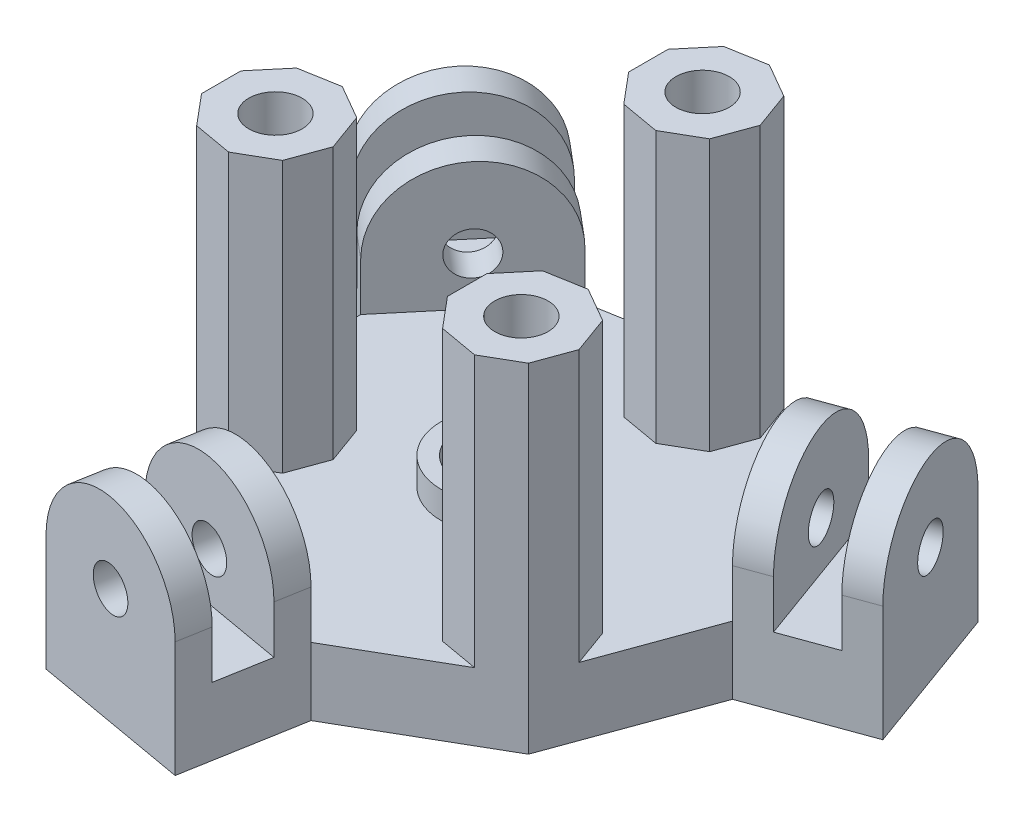
SolidWorks part; units mm, degrees
ref_plane "Front Plane" through (0, 0, 0) normal (0, 0, 1) x (1, 0, 0)
ref_plane "Top Plane" through (0, 0, 0) normal (0, 1, 0) x (1, 0, 0)
ref_plane "Right Plane" through (0, 0, 0) normal (1, 0, 0) x (0, 0, -1)
sketch "Sketch1" plane through (0, 0, 0) normal (0, 1, 0) x (1, 0, 0)
  line L0 (-20.5, -7.4614) -> (-10.9078, -18.8929)
  line L1 (16.7118, -14.0228) -> (21.8156, 0)
  line L2 (21.8156, 0) -> (16.7118, 14.0228)
  line L3 (16.7118, 14.0228) -> (3.7882, 21.4842)
  line L4 (3.7882, 21.4842) -> (-10.9078, 18.8929)
  line L5 (-10.9078, 18.8929) -> (-20.5, 7.4614)
  line L6 (-20.5, 7.4614) -> (-20.5, -7.4614)
  line L7 (-10.9078, -18.8929) -> (3.7882, -21.4842)
  line L8 (3.7882, -21.4842) -> (16.7118, -14.0228)
  line L9 (16.7118, 14.0228) -> (21.8156, 0)
  line L10 (16.7118, 14.0228) -> (27.0484, 17.785)
  line L11 (21.8156, 0) -> (32.1523, 3.7622)
  line L12 (27.0484, 17.785) -> (32.1523, 3.7622)
  line L13 (3.7882, -21.4842) -> (-10.9078, -18.8929)
  line L14 (3.7882, -21.4842) -> (1.8781, -32.3171)
  line L15 (-10.9078, -18.8929) -> (-12.818, -29.7258)
  line L16 (1.8781, -32.3171) -> (-12.818, -29.7258)
  line L17 (-20.5, 7.4614) -> (-10.9078, 18.8929)
  line L18 (-20.5, 7.4614) -> (-28.9265, 14.5321)
  line L19 (-10.9078, 18.8929) -> (-19.3343, 25.9636)
  line L20 (-28.9265, 14.5321) -> (-19.3343, 25.9636)
  circle A0 centre (0, 0) radius 20.5 construction
  circle A1 centre (0, 0) radius 4.1
  dimension "D1" = 41
  dimension "D2" = 8.2
  dimension "D3" = 11
extrude "Boss-Extrude1" add sketch "Sketch1" along normal blind 6.35 contours L16 L14 L7 L15 | L7 L8 L1 L2 L3 L4 L5 L6 L0 A1 | L12 L10 L2 L11 | L20 L18 L5 L19
ref_plane "Plane1" through (-5.4699, 0, 31.0214) normal (0.1736, 0, -0.9848) x (-0.9848, 0, -0.1736)
sketch "Sketch4" plane through (-5.4699, 0, 31.0214) normal (0.1736, 0, -0.9848) x (-0.9848, 0, -0.1736)
  line L0 (-7.4614, 6.35) -> (-7.4614, 10.85)
  line L1 (7.4614, 6.35) -> (7.4614, 10.85)
  line L2 (-7.4614, 6.35) -> (7.4614, 6.35)
  arc A0 (7.4614, 10.85) -> (-7.4614, 10.85) centre (0, 10.85) ccw
  circle A1 centre (0, 10.85) radius 2
  dimension "D2" = 4
  dimension "D1" = 4.5
extrude "Boss-Extrude2" add sketch "Sketch4" along normal blind 3
ref_plane "Plane2" through (-3.5598, 0, 20.1886) normal (0.1736, 0, -0.9848) x (-0.9848, 0, -0.1736)
sketch "Sketch6" plane through (-3.5598, 0, 20.1886) normal (0.1736, 0, -0.9848) x (-0.9848, 0, -0.1736)
  line L0 (-7.4614, 6.35) -> (-7.4614, 10.85)
  line L1 (7.4614, 6.35) -> (7.4614, 10.85)
  line L2 (-7.4614, 6.35) -> (7.4614, 6.35)
  arc A0 (7.4614, 10.85) -> (-7.4614, 10.85) centre (0, 10.85) ccw
  circle A1 centre (0, 10.85) radius 2
  dimension "D2" = 4
  dimension "D1" = 4.5
extrude "Boss-Extrude4" add sketch "Sketch6" against normal blind 3
ref_plane "Plane3" through (29.6003, 0, -10.7736) normal (-0.9397, 0, 0.342) x (0.342, 0, 0.9397)
sketch "Sketch8" plane through (29.6003, 0, -10.7736) normal (-0.9397, 0, 0.342) x (0.342, 0, 0.9397)
  line L0 (-7.4614, 10.85) -> (-7.4614, 6.35)
  line L1 (-7.4614, 6.35) -> (7.4614, 6.35)
  line L2 (7.4614, 6.35) -> (7.4614, 10.85)
  arc A0 (7.4614, 10.85) -> (-7.4614, 10.85) centre (0, 10.85) ccw
  circle A1 centre (0, 10.85) radius 2
  dimension "D2" = 4
  dimension "D1" = 4.5
extrude "Boss-Extrude5" add sketch "Sketch8" along normal blind 3
ref_plane "Plane4" through (19.2637, 0, -7.0114) normal (-0.9397, 0, 0.342) x (0.342, 0, 0.9397)
sketch "Sketch9" plane through (19.2637, 0, -7.0114) normal (-0.9397, 0, 0.342) x (0.342, 0, 0.9397)
  line L0 (-7.4614, 6.35) -> (-7.4614, 10.85)
  line L1 (-7.4614, 6.35) -> (7.4614, 6.35)
  line L2 (7.4614, 6.35) -> (7.4614, 10.85)
  arc A0 (-7.4614, 10.85) -> (7.4614, 10.85) centre (0, 10.85) cw
  circle A1 centre (0, 10.85) radius 2
  dimension "D2" = 4
  dimension "D1" = 4.5
extrude "Boss-Extrude6" add sketch "Sketch9" against normal blind 3
ref_plane "Plane5" through (-24.1304, 0, -20.2478) normal (0.766, 0, 0.6428) x (0.6428, 0, -0.766)
sketch "Sketch10" plane through (-24.1304, 0, -20.2478) normal (0.766, 0, 0.6428) x (0.6428, 0, -0.766)
  line L0 (-7.4614, 10.85) -> (-7.4614, 6.35)
  line L1 (-7.4614, 6.35) -> (7.4614, 6.35)
  line L2 (7.4614, 6.35) -> (7.4614, 10.85)
  arc A0 (7.4614, 10.85) -> (-7.4614, 10.85) centre (0, 10.85) ccw
  circle A1 centre (0, 10.85) radius 2
  dimension "D2" = 4
  dimension "D1" = 4.5
extrude "Boss-Extrude7" add sketch "Sketch10" along normal blind 3
ref_plane "Plane6" through (-15.7039, 0, -13.1771) normal (0.766, 0, 0.6428) x (0.6428, 0, -0.766)
sketch "Sketch11" plane through (-15.7039, 0, -13.1771) normal (0.766, 0, 0.6428) x (0.6428, 0, -0.766)
  line L0 (-7.4614, 10.85) -> (-7.4614, 6.35)
  line L1 (-7.4614, 6.35) -> (7.4614, 6.35)
  line L2 (7.4614, 6.35) -> (7.4614, 10.85)
  arc A0 (7.4614, 10.85) -> (-7.4614, 10.85) centre (0, 10.85) ccw
  circle A1 centre (0, 10.85) radius 2
  dimension "D2" = 4
  dimension "D1" = 4.5
extrude "Boss-Extrude8" add sketch "Sketch11" against normal blind 3
ref_plane "Plane7" through (0, 6.35, 0) normal (0, 1, 0) x (1, 0, 0)
sketch "Sketch12" plane through (0, 6.35, 0) normal (0, 1, 0) x (1, 0, 0)
  line L9 (16.7118, -14.0228) -> (21.8156, 0) construction
  line L29 (16.7118, -14.0228) -> (17.9765, -10.5479)
  line L38 (17.9765, -10.5479) -> (16.7118, -7.073)
  line L48 (6.9908, 12.6854) -> (8.2555, 16.1603)
  line L49 (3.7882, 21.4842) -> (0.1465, 20.8421)
  line L50 (0.1465, 20.8421) -> (-2.2305, 18.0093)
  line L51 (-2.2305, 18.0093) -> (-2.2305, 14.3114)
  line L52 (-2.2305, 14.3114) -> (0.1465, 11.4786)
  line L53 (0.1465, 11.4786) -> (3.7882, 10.8364)
  line L54 (3.7882, 10.8364) -> (6.9908, 12.6854)
  line L55 (8.2555, 16.1603) -> (6.9908, 19.6352)
  line L56 (6.9908, 19.6352) -> (3.7882, 21.4842)
  line L57 (16.7118, -7.073) -> (13.5092, -5.224)
  line L58 (13.5092, -5.224) -> (9.8675, -5.8661)
  line L59 (9.8675, -5.8661) -> (7.4905, -8.6989)
  line L60 (7.4905, -8.6989) -> (7.4905, -12.3969)
  line L61 (7.4905, -12.3969) -> (9.8675, -15.2297)
  line L62 (9.8675, -15.2297) -> (13.5092, -15.8718)
  line L63 (13.5092, -15.8718) -> (16.7118, -14.0228)
  line L64 (-20.5, -7.4614) -> (-10.9078, -18.8929) construction
  line L65 (3.7882, -21.4842) -> (16.7118, -14.0228) construction
  line L66 (-20.5, -7.4614) -> (-18.123, -10.2942)
  line L67 (-18.123, -10.2942) -> (-14.4813, -10.9363)
  line L68 (-14.4813, -10.9363) -> (-11.2787, -9.0873)
  line L69 (-11.2787, -9.0873) -> (-10.014, -5.6124)
  line L70 (-10.014, -5.6124) -> (-11.2787, -2.1375)
  line L71 (-11.2787, -2.1375) -> (-14.4813, -0.2885)
  line L72 (-14.4813, -0.2885) -> (-18.123, -0.9307)
  line L73 (-18.123, -0.9307) -> (-20.5, -3.7635)
  line L74 (-20.5, -3.7635) -> (-20.5, -7.4614)
  line L75 (16.7118, 14.0228) -> (3.7882, 21.4842) construction
  circle A0 centre (2.8495, 16.1603) radius 5.08 construction
  circle A1 centre (12.5705, -10.5479) radius 5.08 construction
  circle A2 centre (-15.42, -5.6124) radius 5.08 construction
  circle A3 centre (2.8495, 16.1603) radius 2.5
  circle A4 centre (12.5705, -10.5479) radius 2.5
  circle A5 centre (-15.42, -5.6124) radius 2.5
  point P49 (0, 0)
  dimension "D1" = 10.16
  dimension "D2" = 5
  dimension "D3" = 3
extrude "Boss-Extrude9" add sketch "Sketch12" along normal blind 25.4
ref_plane "Plane8" through (0, 6.35, 0) normal (0, 1, 0) x (1, 0, 0)
sketch "Sketch15" plane through (0, 6.35, 0) normal (0, 1, 0) x (1, 0, 0)
  circle A0 centre (0, 0) radius 4
  circle A2 centre (0, 0) radius 5.5
  dimension "D1" = 8
  dimension "D2" = 11
extrude "Boss-Extrude10" add sketch "Sketch15" along normal blind 2.54
